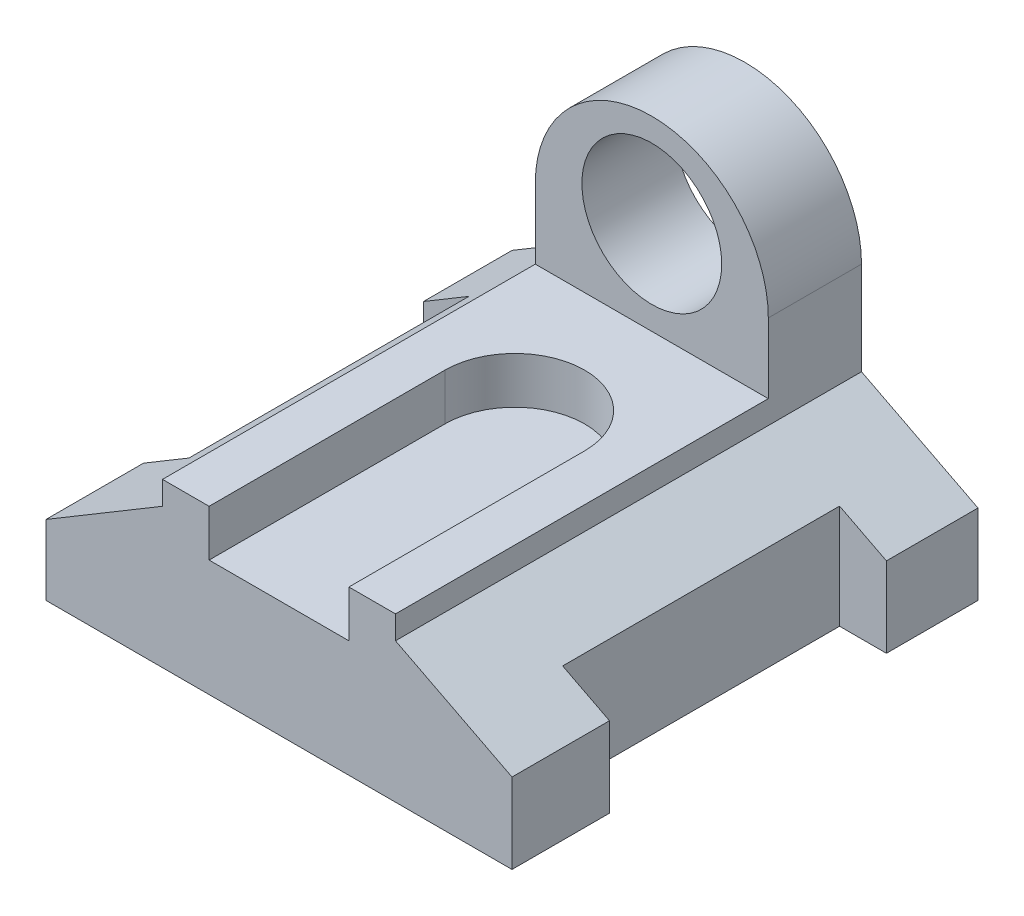
SolidWorks part; units mm, degrees
ref_plane "Front Plane" through (0, 0, 0) normal (0, 0, 1) x (1, 0, 0)
ref_plane "Top Plane" through (0, 0, 0) normal (0, 1, 0) x (1, 0, 0)
ref_plane "Right Plane" through (0, 0, 0) normal (1, 0, 0) x (0, 0, -1)
sketch "Sketch1" plane through (0, 0, 0) normal (0, 0, 1) x (1, 0, 0)
  line L1 (-36.2245, 9.4388) -> (63.7755, 9.4388)
  line L2 (-36.2245, 9.4388) -> (-36.2245, -20.5612)
  line L3 (-36.2245, -20.5612) -> (63.7755, -20.5612)
  line L4 (63.7755, 9.4388) -> (63.7755, -20.5612)
  dimension "D1" = 100
  dimension "D2" = 30
extrude "Boss-Extrude1" add sketch "Sketch1" along normal blind 100
sketch "Sketch2" plane through (0, 0, 0) normal (0, 0, 1) x (1, 0, 0)
  line L0 (-36.2245, 9.4388) -> (-11.2245, 9.4388) construction
  line L1 (63.7755, 9.4388) -> (-36.2245, 9.4388) construction
  line L2 (63.7755, 9.4388) -> (38.7755, 9.4388) construction
  line L3 (-11.2245, 9.4388) -> (-11.2245, 14.4388)
  line L4 (38.7755, 9.4388) -> (38.7755, 14.4388)
  line L5 (-11.2245, 9.4388) -> (38.7755, 9.4388)
  line L6 (38.7755, 14.4388) -> (-11.2245, 14.4388)
  arc A0 (-11.2245, 14.4388) -> (38.7755, 14.4388) centre (13.7755, 14.4388) cw
  dimension "D1" = 25
  dimension "D2" = 25
  dimension "D3" = 5
extrude "Boss-Extrude2" add sketch "Sketch2" along normal blind 100 contours L4 L6 L3 L5
sketch "Sketch3" plane through (0, 0, 0) normal (0, 0, 1) x (1, 0, 0)
  line L0 (-11.2245, 14.4388) -> (38.7755, 14.4388)
  line L1 (-11.2245, 14.4388) -> (-11.2245, 29.4388)
  line L2 (38.7755, 14.4388) -> (38.7755, 29.4388)
  arc A1 (-11.2245, 29.4388) -> (38.7755, 29.4388) centre (13.7755, 29.4388) cw
  dimension "D1" = 15
extrude "Boss-Extrude3" add sketch "Sketch3" along normal blind 20
sketch "Sketch4" plane through (0, 0, 20) normal (0, 0, 1) x (1, 0, 0)
  line L0 (13.7755, 54.4388) -> (13.7755, 14.4388) construction
  line L1 (-11.2245, 14.4388) -> (38.7755, 14.4388) construction
  arc A0 (38.7755, 29.4388) -> (-11.2245, 29.4388) centre (13.7755, 29.4388) ccw construction
  circle A2 centre (13.7755, 34.4388) radius 15
  dimension "D1" = 30
extrude "Cut-Extrude2" cut sketch "Sketch4" against normal blind 20
sketch "Sketch5" plane through (0, 0, 0) normal (0, 1, 0) x (1, 0, 0)
  line L0 (-36.2245, 0) -> (-36.2245, -18.9954) construction
  line L1 (-36.2245, -100) -> (-36.2245, 0) construction
  line L2 (-36.2245, -18.9954) -> (-26.4702, -18.9954) construction
  line L3 (-26.4702, -18.9954) -> (-26.4702, -79.0762) construction
  line L4 (-26.4702, -79.0762) -> (-36.2245, -79.0762) construction
  line L5 (-36.2245, -79.0762) -> (-36.2245, -100) construction
  line L6 (-36.2245, -18.9954) -> (-36.2245, -79.0762)
  line L7 (-36.2245, -79.0762) -> (-26.4702, -79.0762)
  line L8 (-26.4702, -79.0762) -> (-26.4702, -18.9954)
  line L9 (-26.4702, -18.9954) -> (-36.2245, -18.9954)
extrude "Cut-Extrude3" cut sketch "Sketch5" against normal through all both and the other way through all
sketch "Sketch6" plane through (0, 9.4388, 0) normal (0, 1, 0) x (1, 0, 0)
  line L0 (63.7755, 0) -> (63.7755, -19.6515)
  line L1 (63.7755, -100) -> (63.7755, 0) construction
  line L2 (63.7755, -19.6515) -> (53.722, -19.6515)
  line L3 (53.722, -19.6515) -> (53.722, -79.0762)
  line L4 (53.722, -79.0762) -> (63.7755, -79.0762)
  line L5 (63.7755, -79.0762) -> (63.7755, -100)
  line L7 (53.722, -19.6515) -> (63.7755, -19.6515)
  line L8 (53.722, -19.6515) -> (53.722, -79.0762)
  line L9 (53.722, -79.0762) -> (63.7755, -79.0762)
  line L10 (63.7755, -19.6515) -> (63.7755, -79.0762)
  line M4 (63.7755, -100) -> (63.7755, 0)
extrude "Cut-Extrude4" cut sketch "Sketch6" against normal through all both contours L3 L4 L2 M4
sketch "Sketch7" plane through (0, 14.4388, 0) normal (0, 1, 0) x (1, 0, 0)
  line L0 (-11.2245, -100) -> (-1.2245, -100)
  line L1 (38.7755, -100) -> (-11.2245, -100) construction
  line L2 (38.7755, -100) -> (28.7755, -100)
  line L3 (-1.2245, -100) -> (-1.2245, -90)
  line L4 (28.7755, -100) -> (28.7755, -90)
  line L5 (-1.2245, -100) -> (28.7755, -100)
  line L6 (-1.2245, -90) -> (-1.2245, -49.3959)
  line L7 (28.7755, -90) -> (28.7755, -49.3959)
  arc A0 (-1.2245, -49.3959) -> (28.7755, -49.3959) centre (13.7755, -49.3959) cw
  line M7 (-11.2245, -100) -> (38.7755, -100)
  dimension "D1" = 10
  dimension "D2" = 10
  dimension "D3" = 10
extrude "Cut-Extrude5" cut sketch "Sketch7" against normal blind 10 contours A0 L6 L3 L4 L7 M7
sketch "Sketch8" plane through (0, 0, 100) normal (0, 0, 1) x (1, 0, 0)
  line L1 (-36.2245, 9.4388) -> (-36.2245, -20.5612) construction
  line L6 (63.7755, -20.5612) -> (63.7755, 9.4388) construction
  line L8 (-36.2245, 3.2515) -> (-36.2245, 9.4388)
  line L9 (-36.2245, 9.4388) -> (-23.7245, 9.4388)
  line L10 (-11.2245, 9.4388) -> (-36.2245, 9.4388) construction
  line L11 (-36.2245, 3.2515) -> (-23.7245, 9.4388)
  line L13 (63.7755, 9.4388) -> (63.7755, 3.2515)
  line L16 (63.7755, 9.4388) -> (38.7755, 9.4388) construction
  line L17 (51.2755, 9.4388) -> (51.2755, 8.8452)
  line L18 (51.2755, 9.4388) -> (63.7755, 9.4388)
  line L19 (63.7755, 3.2515) -> (51.2755, 9.4388)
  line M9 (63.7755, -20.5612) -> (63.7755, 9.4388)
  line M10 (63.7755, 9.4388) -> (38.7755, 9.4388)
extrude "Cut-Extrude9" cut sketch "Sketch8" against normal blind 130 contours L19 M9 M10 | L9 L11 L8
sketch "Sketch9" plane through (0, 0, 100) normal (0, 0, 1) x (1, 0, 0)
  line L0 (-11.2245, 9.4388) -> (-36.2245, -5.5083)
  line L1 (-36.2245, 3.2515) -> (-36.2245, -20.5612) construction
  line L2 (-36.2245, -5.5083) -> (-36.2245, 9.2739)
  line L4 (38.7755, 9.4388) -> (67.9259, 9.4388)
  line L5 (67.9259, 9.4388) -> (67.9259, -5.5083)
  line L6 (67.9259, -5.5083) -> (38.7755, 9.4388)
  line L7 (-11.2245, 9.4388) -> (-21.8181, 14.3719)
  line L8 (-21.8181, 14.3719) -> (-36.2245, 9.2739)
extrude "Cut-Extrude11" cut sketch "Sketch9" against normal blind 130
